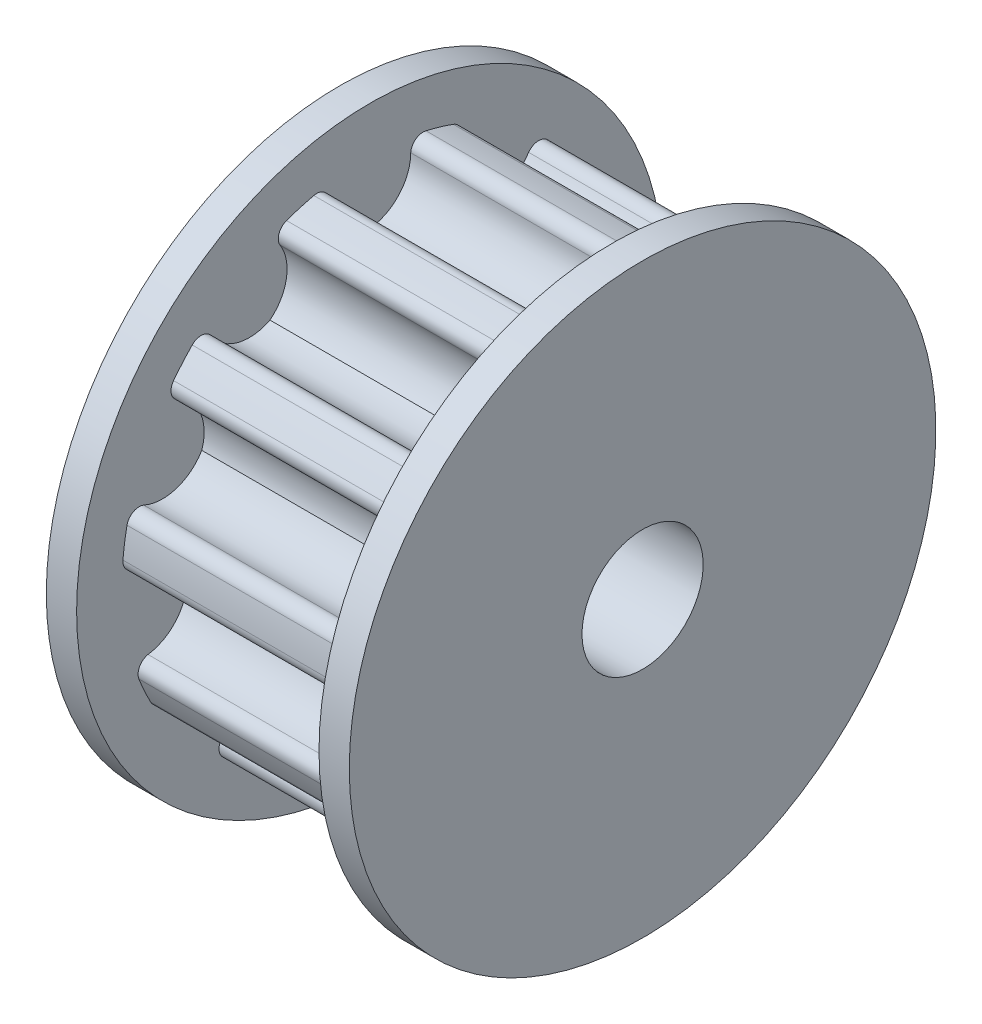
SolidWorks part; units mm, degrees
ref_plane "Front" through (0, 0, 0) normal (0, 0, 1) x (1, 0, 0)
ref_plane "Top" through (0, 0, 0) normal (0, 1, 0) x (1, 0, 0)
ref_plane "Right" through (0, 0, 0) normal (1, 0, 0) x (0, 0, -1)
sketch "Sketch1" plane through (0, 0, 0) normal (1, 0, 0) x (0, 0, -1)
  circle A0 centre (0, 0) radius 8.18
  dimension "D1" = 16.36
extrude "Boss-Extrude1" add sketch "Sketch1" along normal blind 8
sketch "Sketch2" plane through (0, 0, 0) normal (1, 0, 0) x (0, 0, -1)
  line L0 (0, 8.913) -> (0, 0) construction
  arc A0 (0, 6.1) -> (1.348, 7.5923) centre (-0.152, 7.5923) ccw
  arc A1 (1.348, 7.5923) -> (1.85, 7.9681) centre (1.7573, 7.5687) cw
  circle A2 centre (0, 0) radius 8.18 construction
  arc A3 (-1.348, 7.5923) -> (-1.85, 7.9681) centre (-1.7573, 7.5687) ccw
  arc A4 (0, 6.1) -> (-1.348, 7.5923) centre (0.152, 7.5923) cw
  arc A5 (-1.85, 7.9681) -> (1.85, 7.9681) centre (0, 0) cw
  point P7 (1.85, 7.9681)
  point P8 (0, 6.1)
  dimension "D1" = 0.41
  dimension "D4" = 2.08
  dimension "D2" = 1.5
  dimension "D3" = 1.85
extrude "Cut-Extrude1" cut sketch "Sketch2" along normal through all
pattern_circular "CirPattern1" count 11 over 360 about axis through (0, 0, 0) along (1, 0, 0) of "Cut-Extrude1"
ref_plane "Plane1" through (4, 0, 0) normal (-1, 0, 0) x (0, 0, 1)
sketch "Sketch4" plane through (0, 0, 0) normal (-1, 0, 0) x (0, 0, 1)
  circle A0 centre (0, 0) radius 9.68
  arc A1 (6.4795, 4.9929) -> (5.8642, 5.703) centre (0, 0) ccw construction
  dimension "D1" = 1.5
extrude "Boss-Extrude2" add sketch "Sketch4" along normal blind 1
mirror "Mirror1" about plane through (4, 0, 0) normal (-1, 0, 0) of "Boss-Extrude2"
sketch "Sketch6" plane through (-1, 0, 0) normal (-1, 0, 0) x (0, 0, 1)
  circle A0 centre (0, 0) radius 2
  dimension "D1" = 4
extrude "Cut-Extrude2" cut sketch "Sketch6" against normal through all
